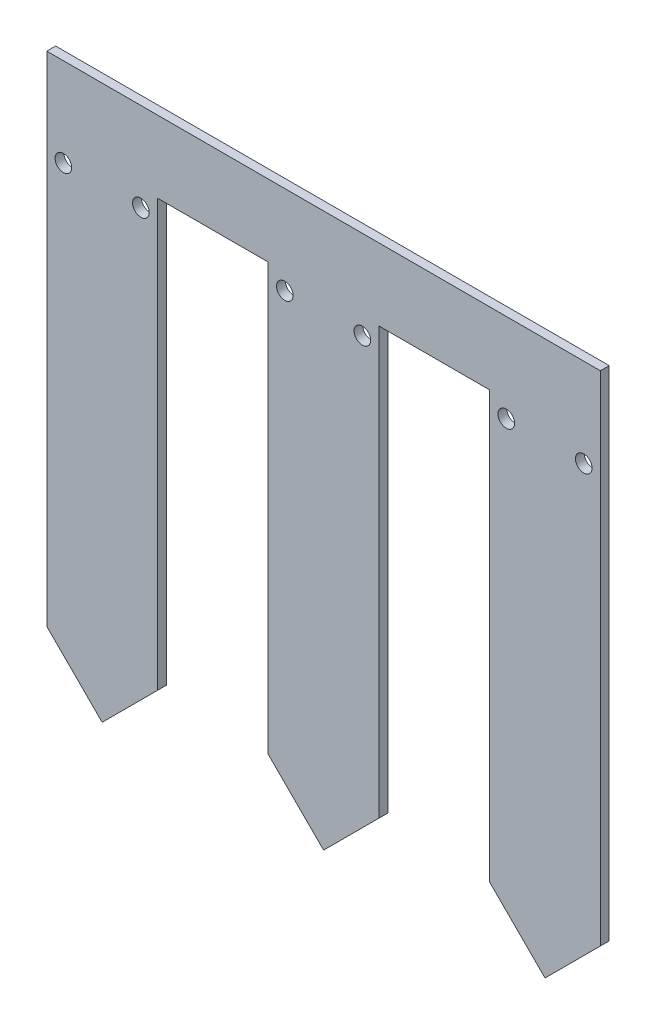
SolidWorks part; units mm, degrees
ref_plane "Ön Düzlem" through (0, 0, 0) normal (0, 0, 1) x (1, 0, 0)
ref_plane "Üst Düzlem" through (0, 0, 0) normal (0, 1, 0) x (1, 0, 0)
ref_plane "Sağ Düzlem" through (0, 0, 0) normal (1, 0, 0) x (0, 0, -1)
sketch "Çizim1" plane through (0, 0, 0) normal (0, 0, 1) x (1, 0, 0)
  line L0 (0, -55) -> (-10, -45)
  line L1 (-10, 45) -> (10, 45)
  line L2 (-10, 45) -> (-10, -45)
  line L4 (10, 32) -> (10, -45)
  line L5 (0, -55) -> (10, -45)
  line L6 (10, 32) -> (30, 32)
  line L7 (30, 32) -> (30, -45)
  line L8 (30, -45) -> (40, -55)
  line L9 (40, -55) -> (50, -45)
  line L10 (50, -45) -> (50, 32)
  line L11 (10, 45) -> (90, 45)
  line L12 (50, 32) -> (70, 32)
  line L13 (70, 32) -> (70, -45)
  line L14 (70, -45) -> (80, -55)
  line L15 (80, -55) -> (90, -45)
  line L16 (90, -45) -> (90, 45)
  circle A0 centre (-7, 29) radius 1.5
  circle A1 centre (7, 29) radius 1.5
  circle A2 centre (33, 29) radius 1.5
  circle A3 centre (47, 29) radius 1.5
  circle A4 centre (73, 29) radius 1.5
  circle A5 centre (87, 29) radius 1.5
  point P4 (0, 45)
  point P6 (-10, 0)
  point P29 (0, 0)
  dimension "D3" = 3
  dimension "D4" = 3
  dimension "D21" = 3
  dimension "D23" = 100
  dimension "D1" = 90
  dimension "D2" = 20
  dimension "D5" = 84
  dimension "D6" = 3
  dimension "D7" = 3
  dimension "D8" = 10
  dimension "D9" = 90
  dimension "D10" = 20
  dimension "D11" = 20
  dimension "D12" = 90
  dimension "D13" = 10
  dimension "D14" = 3
  dimension "D15" = 3
  dimension "D16" = 20
  dimension "D17" = 77
  dimension "D18" = 90
  dimension "D19" = 10
  dimension "D20" = 90
  dimension "D22" = 3
extrude "Yükseklik-Ekstrüzyon1" add sketch "Çizim1" along normal blind 1.6
